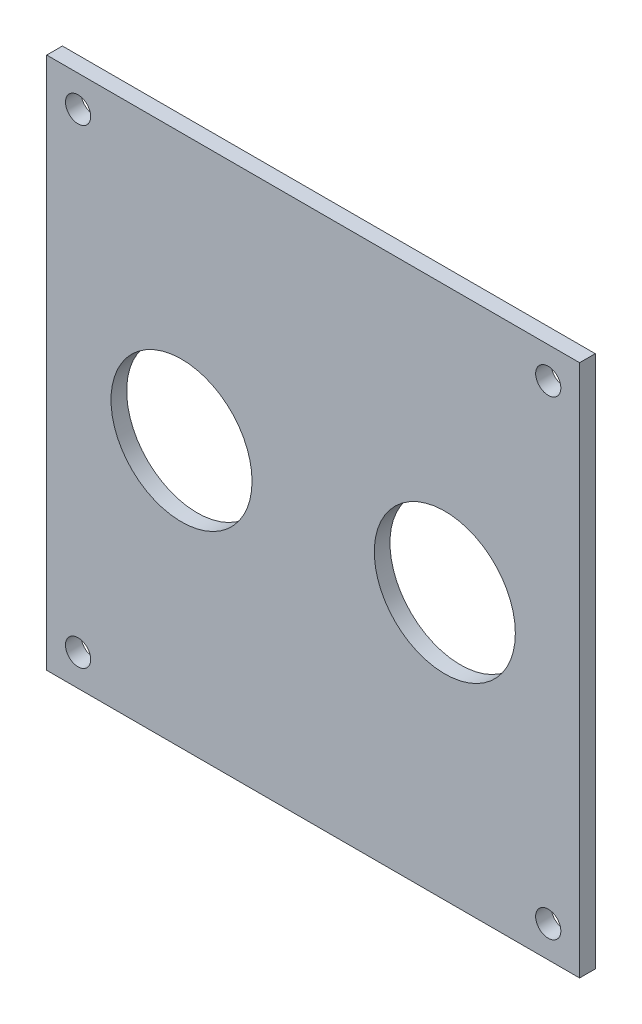
SolidWorks part; units mm, degrees
ref_plane "Front Plane" through (0, 0, 0) normal (0, 0, 1) x (1, 0, 0)
ref_plane "Top Plane" through (0, 0, 0) normal (0, 1, 0) x (1, 0, 0)
ref_plane "Right Plane" through (0, 0, 0) normal (1, 0, 0) x (0, 0, -1)
sketch "Sketch1" plane through (0, 0, 0) normal (0, 0, 1) x (1, 0, 0)
  line L1 (0, 0) -> (107.95, 0)
  line L2 (0, 0) -> (0, 107.95)
  line L3 (0, 107.95) -> (107.95, 107.95)
  line L4 (107.95, 0) -> (107.95, 107.95)
  dimension "D1" = 107.95
extrude "Boss-Extrude1" add sketch "Sketch1" along normal blind 3.175
sketch "Sketch2" plane through (0, 0, 0) normal (0, 0, -1) x (-1, 0, 0)
  line L0 (0, 107.95) -> (0, 0) construction
  line L1 (0, 0) -> (-107.95, 0) construction
  line L2 (-107.95, 0) -> (-107.95, 107.95) construction
  line L3 (-107.95, 107.95) -> (0, 107.95) construction
  circle A0 centre (-6.35, 101.6) radius 2.5527
  circle A1 centre (-101.6, 101.6) radius 2.5527
  circle A2 centre (-101.6, 6.35) radius 2.5527
  circle A3 centre (-6.35, 6.35) radius 2.5527
  dimension "D1" = 5.1054
  dimension "D2" = 5.1054
  dimension "D3" = 5.1054
  dimension "D4" = 5.1054
  dimension "D5" = 6.35
  dimension "D6" = 6.35
  dimension "D7" = 6.35
  dimension "D8" = 6.35
  dimension "D9" = 6.35
  dimension "D10" = 6.35
  dimension "D11" = 6.35
  dimension "D12" = 6.35
extrude "Cut-Extrude1" cut sketch "Sketch2" against normal blind 3.175
sketch "Sketch3" plane through (0, 0, 3.175) normal (0, 0, 1) x (1, 0, 0)
  line L3 (0, 107.95) -> (0, 0) construction
  line L4 (107.95, 107.95) -> (0, 107.95) construction
  circle A0 centre (27.305, 53.975) radius 14.2875
  circle A1 centre (80.645, 53.975) radius 14.2875
  point P4 (0, 53.975)
  dimension "D1" = 28.575
  dimension "D2" = 53.34
  dimension "D3" = 27.305
  dimension "D4" = 53.975
extrude "Cut-Extrude2" cut sketch "Sketch3" against normal blind 3.175
